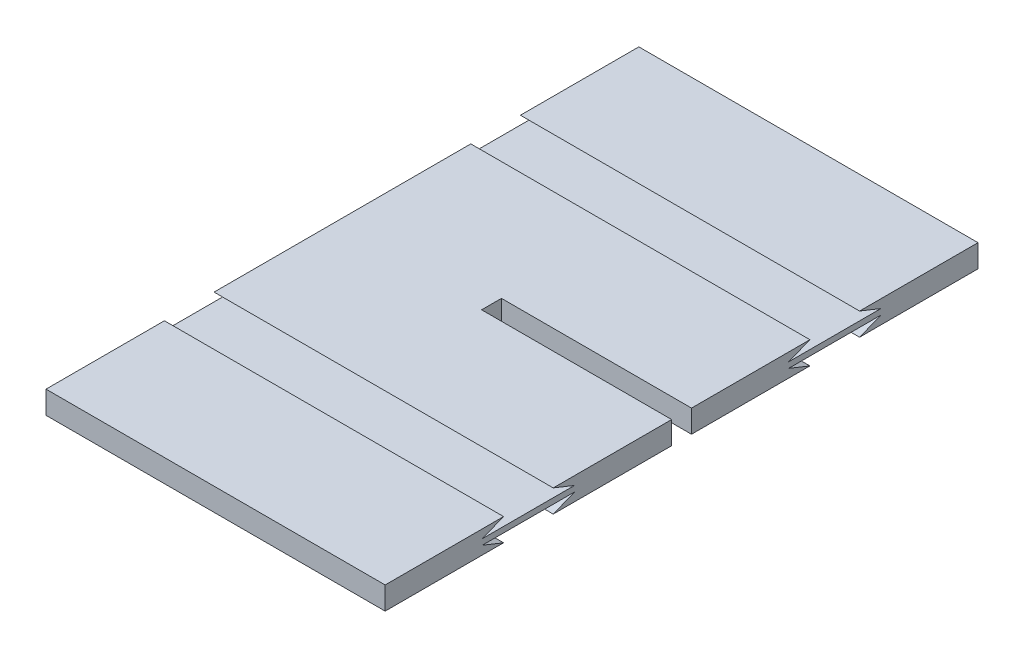
SolidWorks part; units mm, degrees
ref_plane "Front Plane" through (0, 0, 0) normal (0, 0, 1) x (1, 0, 0)
ref_plane "Top Plane" through (0, 0, 0) normal (0, 1, 0) x (1, 0, 0)
ref_plane "Right Plane" through (0, 0, 0) normal (1, 0, 0) x (0, 0, -1)
sketch "Sketch1" plane through (0, 0, 0) normal (0, 1, 0) x (1, 0, 0)
  line L0 (-13.4782, 10.45) -> (13.4782, 10.45)
  line L1 (-13.5782, -10.55) -> (13.5782, -10.55)
  line L2 (-13.5782, -10.55) -> (-13.5782, 10.55)
  line L3 (-13.5782, 10.55) -> (13.5782, 10.55)
  line L4 (13.5782, -10.55) -> (13.5782, 10.55)
  line L5 (-13.5782, -10.55) -> (13.5782, 10.55) construction
  line L6 (-13.5782, 10.55) -> (13.5782, -10.55) construction
  line L7 (13.4782, -10.45) -> (13.4782, 10.45)
  line L8 (-13.4782, -10.45) -> (13.4782, -10.45)
  line L9 (-13.4782, -10.45) -> (-13.4782, 10.45)
  line L10 (0, 0) -> (13.4782, 0) construction
  line L11 (13.4782, 0.35) -> (-8.2218, 0.35)
  line L12 (13.4782, -0.35) -> (-8.2218, -0.35)
  line L13 (-8.2218, -0.35) -> (-8.2218, 0.35)
  point P0 (0, 0)
  point P12 (13.4782, 0.35)
  dimension "D1" = 0.1
extrude "Boss-Extrude1" add sketch "Sketch1" along normal blind 0.8 contours L12 L13 L11 L7 L0 L9 L8
sketch "Sketch2" plane through (13.4782, 0, 0) normal (1, 0, 0) x (0, 0, -1)
  line L0 (-5.4, 0.8) -> (-5.4, 0) construction
  line L1 (-10.45, 0.8) -> (-0.35, 0.8) construction
  line L2 (-10.45, 0) -> (-0.35, 0) construction
  line L3 (-10.45, 0.4) -> (-0.35, 0.4) construction
  line L4 (-10.45, 0.8) -> (-10.45, 0) construction
  line L5 (-0.35, 0.8) -> (-0.35, 0) construction
  line L6 (-7.025, 0.5) -> (-3.775, 0.5)
  line L7 (-3.775, 0.5) -> (-4.525, 0.8)
  line L8 (-7.025, 0.5) -> (-6.275, 0.8)
  line L9 (-6.275, 0.8) -> (-4.525, 0.8)
  line L10 (-7.025, 0.3) -> (-6.275, 0)
  line L11 (-7.025, 0.3) -> (-3.775, 0.3)
  line L12 (-3.775, 0.3) -> (-4.525, 0)
  line L13 (-6.275, 0) -> (-4.525, 0)
  line L14 (0, 0) -> (0, 0.8) construction
  line L15 (7.025, 0.3) -> (3.775, 0.3)
  line L16 (3.775, 0.3) -> (4.525, 0)
  line L17 (6.275, 0) -> (4.525, 0)
  line L18 (7.025, 0.3) -> (6.275, 0)
  line L19 (7.025, 0.5) -> (6.275, 0.8)
  line L20 (7.025, 0.5) -> (3.775, 0.5)
  line L21 (3.775, 0.5) -> (4.525, 0.8)
  line L22 (6.275, 0.8) -> (4.525, 0.8)
  point P13 (-5.4, 0.5)
  point P14 (-5.4, 0.5)
  point P15 (-5.4, 0.5)
  point P16 (-5.4, 0.5)
  point P17 (-4.525, 0.8)
extrude "Cut-Extrude1" cut sketch "Sketch2" against normal blind 21.7 from offset 5.3 offset against normal yes
sketch "Sketch3" plane through (0, 0.8, 0) normal (0, 1, 0) x (1, 0, 0)
  line L0 (13.4782, -10.45) -> (-1.5218, -10.45)
  line L1 (-13.4782, -10.45) -> (13.4782, -10.45) construction
  line L2 (-1.5218, -10.45) -> (-1.5218, 10.45)
  line L3 (-13.4782, 10.45) -> (13.4782, 10.45) construction
  line L4 (-1.5218, 10.45) -> (13.4782, 10.45)
  line L5 (13.4782, 10.45) -> (13.4782, -10.45)
extrude "Cut-Extrude2" cut sketch "Sketch3" against normal through all
